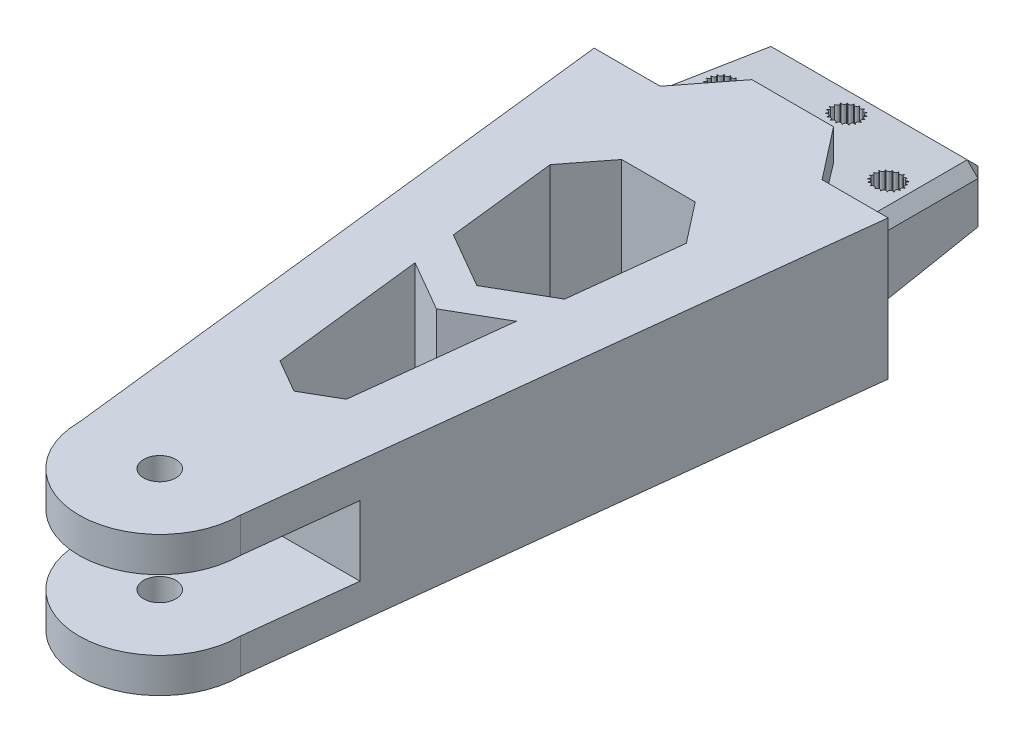
SolidWorks part; units mm, degrees
material "ABS"
ref_plane "Front Plane" through (0, 0, 0) normal (0, 0, 1) x (1, 0, 0)
ref_plane "Top Plane" through (0, 0, 0) normal (0, 1, 0) x (1, 0, 0)
ref_plane "Right Plane" through (0, 0, 0) normal (1, 0, 0) x (0, 0, -1)
sketch "Sketch2" plane through (0, 0, 0) normal (0, 1, 0) x (1, 0, 0)
  line L0 (0, 0) -> (0, 3) construction
  line L1 (0, 175) -> (168.3275, 175) construction
  line L2 (168.3275, 175) -> (-205.8504, 175) construction
  line L3 (-15, 350) -> (-35, 175)
  line L4 (-35, 175) -> (-15, 0)
  line L5 (15, 350) -> (35, 175)
  line L6 (35, 175) -> (15, 0)
  line L7 (0, 335) -> (0, 350) construction
  line L8 (31.3255, 207.1517) -> (24.2545, 200.0806)
  line L9 (24.2545, 200.0806) -> (24.2545, 149.9194)
  line L10 (31.3255, 142.8483) -> (24.2545, 149.9194)
  line L11 (-31.3255, 142.8483) -> (-24.2545, 149.9194)
  line L12 (-24.2545, 200.0806) -> (-24.2545, 149.9194)
  line L13 (-31.3255, 207.1517) -> (-24.2545, 200.0806)
  circle A0 centre (0, 350) radius 3
  circle A1 centre (0, 0) radius 3
  arc A2 (15, 350) -> (-15, 350) centre (0, 350) ccw
  arc A3 (-15, 0) -> (15, 0) centre (0, 0) ccw
  circle A4 centre (0, 175) radius 5
  point P21 (24.2545, 175)
  dimension "D2" = 6
  dimension "D3" = 6
  dimension "D4" = 30
  dimension "D5" = 30
  dimension "D7" = 10
  dimension "D1" = 350
  dimension "D6" = 35
  dimension "D8" = 32.1517
  dimension "D9" = 10
extrude "Boss-Extrude1" add sketch "Sketch2" along normal blind 26 contours L4 A3 L6 L10 L9 L8 L5 A2 L3 L13 L12 L11 A4 A0 A1
sketch "Sketch3" plane through (0, 0, 0) normal (1, 0, 0) x (0, 0, -1)
  line L0 (-15, 13) -> (370.2756, 13) construction
  line L1 (-15, 26) -> (-15, 0) construction
  line L3 (177.6378, 13) -> (177.6378, -89.1144) construction
  line L5 (-50, 19.5) -> (20, 19.5)
  line L6 (-50, 19.5) -> (-50, 6.5)
  line L7 (-50, 6.5) -> (20, 6.5)
  line L8 (20, 19.5) -> (20, 6.5)
  line L9 (-50, 19.5) -> (20, 6.5) construction
  line L10 (-50, 6.5) -> (20, 19.5) construction
  dimension "D1" = 13
  dimension "D2" = 35
extrude "Cut-Extrude1" cut sketch "Sketch3" against normal mid plane 55
sketch "Sketch4" plane through (0, 26, 0) normal (0, 1, 0) x (1, 0, 0)
  circle A0 centre (0, 175) radius 5
sketch "Sketch5" plane through (24.2545, 0, 0) normal (1, 0, 0) x (0, 0, -1)
  line L0 (149.9194, 13) -> (220.8721, 13) construction
  line L1 (149.9194, 26) -> (149.9194, 0) construction
  line L2 (175, 0) -> (175, 36.8039) construction
  line L3 (200.0806, 0) -> (149.9194, 0) construction
  line L4 (142.8483, 26) -> (149.9194, 23.4568)
  line L5 (149.9194, 23.4568) -> (200.0806, 23.4568)
  line L6 (142.8483, 26) -> (207.1517, 26)
  line L7 (207.1517, 26) -> (200.0806, 23.4568)
  line L8 (207.1517, 0) -> (200.0806, 2.5432)
  line L9 (149.9194, 2.5432) -> (200.0806, 2.5432)
  line L10 (142.8483, 0) -> (149.9194, 2.5432)
  line L11 (142.8483, 0) -> (207.1517, 0)
  point P14 (175, 23.4568)
  point P15 (175, 26)
extrude "Cut-Extrude2" cut sketch "Sketch5" against normal mid plane 126
ref_plane "Plane1" through (0, 0, -175) normal (0, 0, 1) x (1, 0, 0)
mirror "Mirror3" about plane through (0, 0, -175) normal (0, 0, 1) of "Cut-Extrude1"
sketch "Sketch7" plane through (0, 26, 0) normal (0, 1, 0) x (1, 0, 0)
  line L0 (-31.3255, 142.8483) -> (31.3255, 142.8483) construction
  line L1 (-31.3255, 142.8483) -> (31.3255, 142.8483) construction
  line L2 (0, 142.8483) -> (0, 73.6656) construction
  line L3 (31.3255, 142.8483) -> (15, 0) construction
  line L4 (7.6, 117.8483) -> (-7.6, 117.8483)
  line L5 (-7.6, 117.8483) -> (-15.0712, 108.2483)
  line L6 (-15.0712, 108.2483) -> (-27.3712, 108.2483)
  line L7 (-31.3255, 142.8483) -> (-15, 0) construction
  line L8 (15.0712, 108.2483) -> (27.3712, 108.2483)
  line L9 (7.6, 117.8483) -> (15.0712, 108.2483)
  line L10 (-27.3712, 108.2483) -> (-64.4913, 177.3827)
  line L11 (-64.4913, 177.3827) -> (-40.6605, 301.0842)
  line L12 (-40.6605, 301.0842) -> (-15.3712, 412.0549)
  line L13 (-15.3712, 412.0549) -> (101.6592, 225.6905)
  line L14 (101.6592, 225.6905) -> (42.0926, 95.1056)
  line L15 (42.0926, 95.1056) -> (27.3712, 108.2483)
  circle A0 centre (0, 127.8483) radius 2
  circle A1 centre (-15.3712, 120.2483) radius 2
  circle A2 centre (15.3712, 120.2483) radius 2
  point P23 (0, 117.8483)
  dimension "D4" = 4
  dimension "D5" = 4
  dimension "D1" = 12.3
  dimension "D2" = 9.6
  dimension "D3" = 25
  dimension "D6" = 12
  dimension "D7" = 12
  dimension "D8" = 7.6
  dimension "D9" = 10
extrude "Cut-Extrude3" cut sketch "Sketch7" against normal blind 101 contours L10 L11 L12 L13 L14 L15 L8 L9 L4 L5 L6
sketch "Sketch8" plane through (0, 0, -117.8483) normal (0, 0, -1) x (-1, 0, 0)
  line L0 (27.3712, 0) -> (27.3712, 26) construction
  line L1 (-22.3712, 21) -> (22.3712, 21)
  line L2 (-22.3712, 21) -> (-22.3712, 5)
  line L3 (-22.3712, 5) -> (22.3712, 5)
  line L4 (22.3712, 21) -> (22.3712, 5)
  line L5 (-22.3712, 21) -> (22.3712, 5) construction
  line L6 (-22.3712, 5) -> (22.3712, 21) construction
  line L7 (-7.6, 0) -> (7.6, 0) construction
  line L8 (-27.3712, 0) -> (-27.3712, 26) construction
  line L9 (15.0712, 26) -> (27.3712, 26) construction
  point P0 (0, 13)
  dimension "D1" = 5
  dimension "D2" = 5
  dimension "D3" = 5
  dimension "D4" = 5
extrude "Boss-Extrude2" add sketch "Sketch8" along normal blind 26 draft 5 from surface at -9.6 starting at face at (21.2212, 13, -108.2483)
sketch "Sketch10" plane through (0, 26, 0) normal (0, 1, 0) x (1, 0, 0)
  line L0 (0, 134.2483) -> (0, 112.0591) construction
  line L1 (20.0965, 134.2483) -> (-20.0965, 134.2483) construction
  circle A1 centre (-15.3712, 120.2483) radius 2 construction
  circle A2 centre (0, 127.8483) radius 2 construction
  circle A4 centre (-15.3712, 120.2483) radius 2
  circle A5 centre (0, 127.8483) radius 2
  circle A6 centre (0, 127.8483) radius 2.75
  circle A7 centre (-2.75, 127.8483) radius 0.4
  circle A8 centre (-2.601, 128.7412) radius 0.4
  circle A9 centre (-2.1701, 129.5374) radius 0.4
  circle A10 centre (-1.5041, 130.1505) radius 0.4
  circle A11 centre (-0.6751, 130.5141) radius 0.4
  circle A12 centre (0.2271, 130.5889) radius 0.4
  circle A13 centre (1.1047, 130.3667) radius 0.4
  circle A14 centre (1.8625, 129.8715) radius 0.4
  circle A15 centre (2.4186, 129.1572) radius 0.4
  circle A16 centre (2.7125, 128.3009) radius 0.4
  circle A17 centre (2.7125, 127.3957) radius 0.4
  circle A18 centre (2.4186, 126.5394) radius 0.4
  circle A19 centre (1.8625, 125.8251) radius 0.4
  circle A20 centre (1.1047, 125.3299) radius 0.4
  circle A21 centre (0.2271, 125.1077) radius 0.4
  circle A22 centre (-0.6751, 125.1824) radius 0.4
  circle A23 centre (-1.5041, 125.5461) radius 0.4
  circle A24 centre (-2.1701, 126.1592) radius 0.4
  circle A25 centre (-2.601, 126.9554) radius 0.4
  circle A26 centre (-15.3712, 120.2483) radius 2.75
  circle A27 centre (-18.1212, 120.2483) radius 0.4
  circle A105 centre (-17.9722, 121.1412) radius 0.4
  circle A106 centre (-17.5414, 121.9374) radius 0.4
  circle A107 centre (-16.8753, 122.5505) radius 0.4
  circle A108 centre (-16.0463, 122.9141) radius 0.4
  circle A109 centre (-15.1441, 122.9889) radius 0.4
  circle A110 centre (-14.2666, 122.7667) radius 0.4
  circle A111 centre (-13.5087, 122.2715) radius 0.4
  circle A112 centre (-12.9527, 121.5572) radius 0.4
  circle A113 centre (-12.6587, 120.7009) radius 0.4
  circle A114 centre (-12.6587, 119.7957) radius 0.4
  circle A115 centre (-12.9527, 118.9394) radius 0.4
  circle A116 centre (-13.5087, 118.2251) radius 0.4
  circle A117 centre (-14.2666, 117.7299) radius 0.4
  circle A118 centre (-15.1441, 117.5077) radius 0.4
  circle A119 centre (-16.0463, 117.5824) radius 0.4
  circle A120 centre (-16.8753, 117.9461) radius 0.4
  circle A121 centre (-17.5414, 118.5592) radius 0.4
  circle A122 centre (-17.9722, 119.3554) radius 0.4
  circle A123 centre (17.9722, 119.3554) radius 0.4
  circle A124 centre (17.5414, 118.5592) radius 0.4
  circle A125 centre (16.8753, 117.9461) radius 0.4
  circle A126 centre (16.0463, 117.5824) radius 0.4
  circle A127 centre (15.1441, 117.5077) radius 0.4
  circle A128 centre (14.2666, 117.7299) radius 0.4
  circle A129 centre (13.5087, 118.2251) radius 0.4
  circle A130 centre (12.9527, 118.9394) radius 0.4
  circle A131 centre (12.6587, 119.7957) radius 0.4
  circle A132 centre (12.6587, 120.7009) radius 0.4
  circle A133 centre (12.9527, 121.5572) radius 0.4
  circle A134 centre (13.5087, 122.2715) radius 0.4
  circle A135 centre (14.2666, 122.7667) radius 0.4
  circle A136 centre (15.1441, 122.9889) radius 0.4
  circle A137 centre (16.0463, 122.9141) radius 0.4
  circle A138 centre (16.8753, 122.5505) radius 0.4
  circle A139 centre (17.5414, 121.9374) radius 0.4
  circle A140 centre (17.9722, 121.1412) radius 0.4
  circle A141 centre (18.1212, 120.2483) radius 0.4
  circle A142 centre (15.3712, 120.2483) radius 2.75
  circle A143 centre (15.3712, 120.2483) radius 2
  dimension "D1" = 5.5
  dimension "D2" = 0.8
  dimension "D4" = 5.5
  dimension "D5" = 0.8
  dimension "D3" = 19
  dimension "D6" = 19
extrude "Cut-Extrude4" cut sketch "Sketch10" against normal blind 4 from surface
chamfer "Chamfer1" distance 2 angle 45 8 edges at (21.2339, 6.1374, -121.2483) (-21.2339, 6.1374, -121.2483) (21.2339, 19.8626, -121.2483) (-21.2339, 19.8626, -121.2483) (-20.0965, 13, -134.2483) (0, 7.2747, -134.2483) (20.0965, 13, -134.2483) (0, 18.7253, -134.2483)
sketch "Sketch11" plane through (0, 26, 0) normal (0, 1, 0) x (1, 0, 0)
  line L0 (0, 0) -> (0, 117.8483) construction
  line L1 (-7.6, 117.8483) -> (7.6, 117.8483) construction
  line L2 (0, 25) -> (-6.1873, 28.5722)
  line L3 (-6.1873, 28.5722) -> (-12.6777, 85.3631)
  line L4 (-12.6777, 85.3631) -> (-6.8523, 92.8483)
  line L5 (-6.8523, 92.8483) -> (6.8523, 92.8483)
  line L6 (-7.6, 117.8483) -> (-15.0712, 108.2483) construction
  line L7 (-27.3712, 108.2483) -> (-15, 0) construction
  line L8 (12.6777, 85.3631) -> (6.8523, 92.8483)
  line L9 (6.1873, 28.5722) -> (12.6777, 85.3631)
  line L10 (0, 25) -> (6.1873, 28.5722)
  line L11 (27.3712, 108.2483) -> (15, 0) construction
  point P15 (0, 92.8483)
  dimension "D1" = 25
  dimension "D2" = 25
  dimension "D3" = 60
  dimension "D4" = 12
extrude "Cut-Extrude6" cut sketch "Sketch11" against normal blind 54
sketch "Sketch12" plane through (0, 26, 0) normal (0, 1, 0) x (1, 0, 0)
  line L0 (0, 0) -> (0, 88.3136) construction
  line L1 (-9.4325, 56.9677) -> (0, 51.5218)
  line L2 (-12.6777, 85.3631) -> (-6.1873, 28.5722) construction
  line L3 (-6.1873, 28.5722) -> (0, 25) construction
  line L4 (-10.3532, 65.024) -> (0, 59.0466)
  line L5 (-9.4325, 56.9677) -> (-10.3532, 65.024)
  line L6 (9.4325, 56.9677) -> (0, 51.5218)
  line L7 (9.4325, 56.9677) -> (10.3532, 65.024)
  line L8 (10.3532, 65.024) -> (0, 59.0466)
extrude "Boss-Extrude3" add sketch "Sketch12" against normal up to surface (26 mm away) up to face at (0, 0, -62.6525)
sketch "Sketch13" plane through (0, 0, 0) normal (0, 1, 0) x (1, 0, 0)
  circle A0 centre (0, 127.8483) radius 2
  circle A1 centre (-15.3712, 120.2483) radius 2
  circle A2 centre (15.3712, 120.2483) radius 2
extrude "Cut-Extrude7" cut sketch "Sketch13" along normal blind 22 contours A2 | A0 | A1
